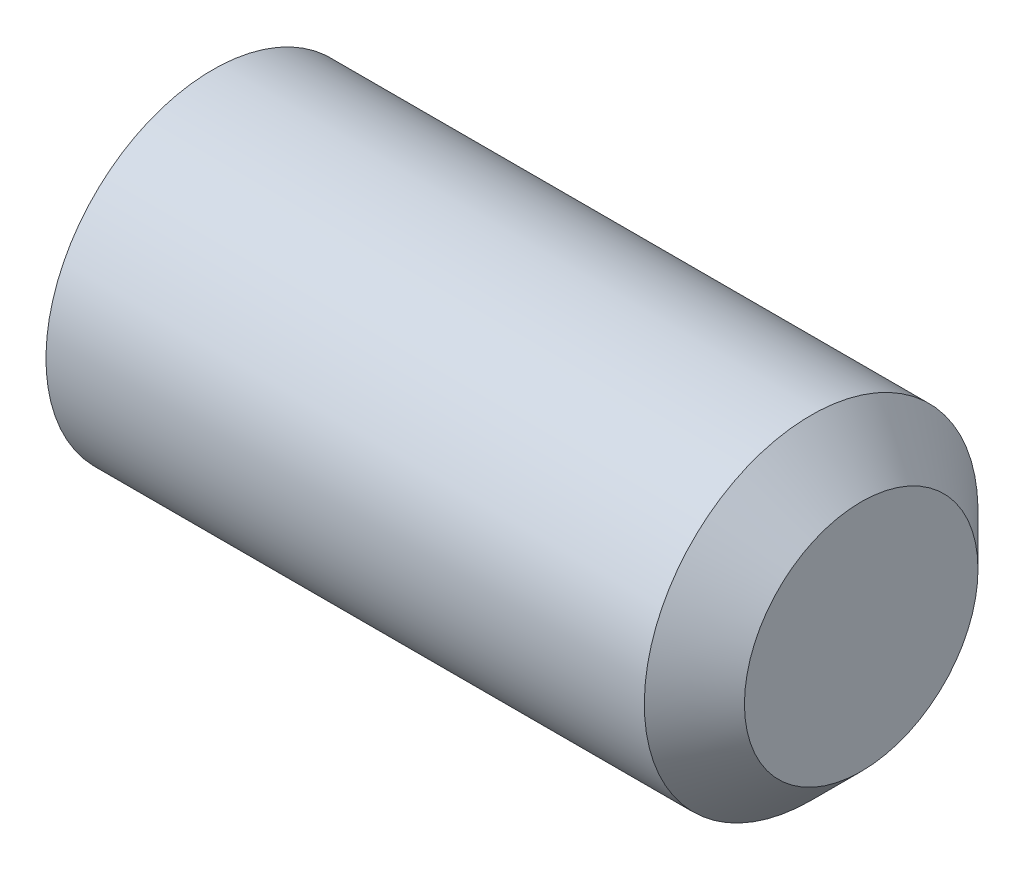
SolidWorks part; units mm, degrees
ref_plane "Front Plane" through (0, 0, 0) normal (0, 0, 1) x (1, 0, 0)
ref_plane "Top Plane" through (0, 0, 0) normal (0, 1, 0) x (1, 0, 0)
ref_plane "Right Plane" through (0, 0, 0) normal (1, 0, 0) x (0, 0, -1)
ref_plane "Plane1" through (0, 0, 0) normal (0, 0, 1) x (1, 0, 0)
sketch "Sketch1" plane through (0, 0, 0) normal (0, 0, 1) x (1, 0, 0)
  line L0 (10, 0) -> (10, -1.75)
  line L1 (10, -1.75) -> (9.25, -2.5)
  line L2 (9.25, -2.5) -> (0.2832, -2.5)
  line L3 (0.2832, -2.5) -> (0, -2.0095)
  line L4 (0, -2.0095) -> (0, -1.4434)
  line L5 (0, -1.4434) -> (0.8333, 0)
  line L6 (0.8333, 0) -> (10, 0)
  line L7 (0.8333, 0) -> (10, 0) construction
revolve "Revolve1" add sketch "Sketch1" angle 360 about L7
ref_plane "Plane2" through (0, 0, 0) normal (1, 0, 0) x (0, 0, -1)
sketch "Sketch2" plane through (0, 0, 0) normal (1, 0, 0) x (0, 0, -1)
  line L0 (-1.4434, 0) -> (-0.7217, -1.25)
  line L1 (-0.7217, -1.25) -> (0.7217, -1.25)
  line L2 (0.7217, -1.25) -> (1.4434, 0)
  line L3 (1.4434, 0) -> (0.7217, 1.25)
  line L4 (0.7217, 1.25) -> (-0.7217, 1.25)
  line L5 (-0.7217, 1.25) -> (-1.4434, 0)
extrude "Cut-Extrude1" cut sketch "Sketch2" along normal blind 3
